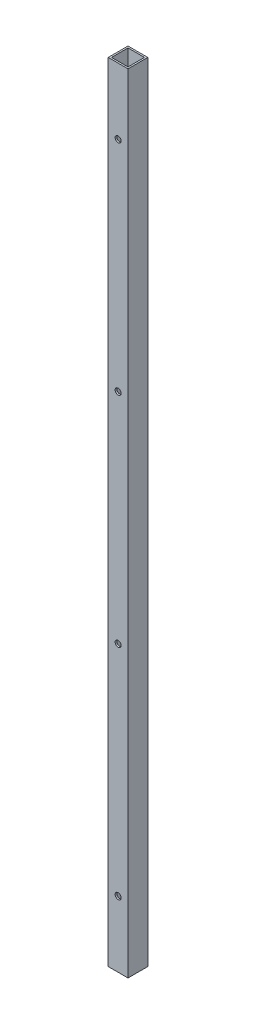
SolidWorks part; units mm, degrees
material "1060 Alloy"
ref_plane "Front Plane" through (0, 0, 0) normal (0, 0, 1) x (1, 0, 0)
ref_plane "Top Plane" through (0, 0, 0) normal (0, 1, 0) x (1, 0, 0)
ref_plane "Right Plane" through (0, 0, 0) normal (1, 0, 0) x (0, 0, -1)
sketch "Sketch1" plane through (0, 0, 0) normal (0, 1, 0) x (1, 0, 0)
  line L1 (-9.525, 9.525) -> (9.525, 9.525)
  line L2 (-9.525, 9.525) -> (-9.525, -9.525)
  line L3 (-9.525, -9.525) -> (9.525, -9.525)
  line L4 (9.525, 9.525) -> (9.525, -9.525)
  line L5 (-9.525, 9.525) -> (9.525, -9.525) construction
  line L6 (-9.525, -9.525) -> (9.525, 9.525) construction
  line L7 (-7.9375, 7.9375) -> (7.9375, 7.9375)
  line L8 (-7.9375, 7.9375) -> (-7.9375, -7.9375)
  line L9 (-7.9375, -7.9375) -> (7.9375, -7.9375)
  line L10 (7.9375, 7.9375) -> (7.9375, -7.9375)
  line L11 (-7.9375, 7.9375) -> (7.9375, -7.9375) construction
  line L12 (-7.9375, -7.9375) -> (7.9375, 7.9375) construction
  point P0 (0, 0)
  point P5 (0, 0)
  dimension "D2" = 19.05
  dimension "D1" = 19.05
  dimension "D3" = 15.875
  dimension "D4" = 15.875
extrude "Tube" add sketch "Sketch1" along normal blind 758.9266
sketch "Sketch2" plane through (0, 0, 9.525) normal (0, 0, 1) x (1, 0, 0)
  line L0 (0, 758.9266) -> (0, 777.9766) construction
  line L1 (0, 777.9766) -> (0, 781.05) construction
  line L6 (0, 695.325) -> (0, 758.9266) construction
  line L7 (-9.525, 758.9266) -> (9.525, 758.9266) construction
  circle A2 centre (0, 695.325) radius 2.8956
  dimension "D1" = 5.7912
  dimension "D2" = 19.05
  dimension "D3" = 3.0734
  dimension "D4" = 85.725
extrude "Side Wall Holes" cut sketch "Sketch2" against normal through all
pattern_linear "LPattern1" count 4 spacing 210.5745 along (0, -1, 0) of "Side Wall Holes"
sketch "Sketch3" plane through (-9.525, 0, 0) normal (-1, 0, 0) x (0, 0, 1)
  line L0 (-9.525, 758.9266) -> (9.525, 758.9266) construction
  line L1 (-123.9293, 379.4633) -> (189.6619, 379.4633) construction
  line L2 (-9.525, 0) -> (9.525, 0) construction
  circle A0 centre (0, 674.37) radius 4.7625
  circle A1 centre (0, 84.5566) radius 4.7625
  point P4 (0, 758.9266)
  dimension "D1" = 9.525
  dimension "D2" = 84.5566
extrude "Cut-Extrude1" cut sketch "Sketch3" against normal up to next and the other way through all
equation "\"Height\"= 32in"
equation "\"Width\"= 23in"
equation "\"Depth\"= 20in"
equation "\"Plexi\"= .121in"
equation "\"Cutwidth\"= .016in"
equation "\"Earsize\"= 1in + \"Cutwidth\" /2"
equation "\"Slotsize\" = 1in - \"CutWidth\" / 2"
equation "\"InnerWidth\" = \"Width\" - 2* \"Plexi\""
equation "\"InnerHeight\" = \"Height\" -2 * \"Plexi\""
equation "\"RearHoleSpacing\" = (\"Width\" - 2*\"RearHolesBorder\") / (\"RearNumHoles\"-1)"
equation "\"RivetDia\" = .228in"
equation "\"SlotDepth\" = \"Plexi\" + 0.75in + .005in"
equation "\"SideSlotWidth\"   = \"Plexi\"+.005in"
equation "\"D1@Sketch2\"=\"RivetDia\""
equation "\"D2@Sketch2\"=\"CornerCube\""
equation "\"SidePanelVertSpacing\" = (\"Height\"-2*(1.75-\"Plexi\")) / 5"
equation "\"MagnetThickness\"= 0.125in"
equation "\"MagnetDiameter\"= 12mm"
equation "\"DoorPlexi\" = \"Plexi\""
equation "\"Boxsize\" = .75in"
equation "\"Boxinner\" = .625in"
equation "\"CornerCube\" = 0.75in"
equation "\"FingerLength\" = 1.125in"
equation "\"InnerDepth\" = \"Depth\" - 2*\"Plexi\""
equation "\"RearNumHoles\" = 4"
equation "\"RearHolesBorder\" = 2.25"
equation "\"RearBarLength\" = (\"InnerWidth\"-2*\"CornerCube\")"
equation "\"RearTopNumHoles\" = 4"
equation "\"RearTopHolesBorder\" = 3.1"
equation "\"RearTopHolesSpacing\" = (\"Width\" - 2*\"RearTopHolesBorder\") / (\"RearTopNumHoles\"-1)"
equation "\"SideTopNumHoles\" = 4"
equation "\"SideTopHoleOffset\"=\"CornerCube\"+\"FingerLength\"+\"Plexi\"+.5"
equation "\"SideTopHoleSpacing\" = (\"TopBarDepth\"-2*\"SideTopHoleOffset\") / (\"SideTopNumHoles\"-1)"
equation "\"SideHorizNumHoles\" = 4"
equation "\"SideHorizHoleBorder\" = 1.50"
equation "\"SideHorizHoleSpacing\" = (\"TopBarDepth\"-2*\"SideHorizHoleBorder\") / (\"SideHorizNumHoles\"-1)"
equation "\"SideVertNumHoles\" = 4"
equation "\"SideVertHolesBorder\" = \"CornerCube\"+\"FingerLength\"+1.50"
equation "\"SideVertHoleSpacing\" = (\"SideVertBarLength\" - 2*(\"SideVertHolesBorder\"-\"Plexi\"-\"CornerCube\")) / (\"SideVertNumHoles\"-1)"
equation "\"BottomPanelSideHoleSpacing\" = (\"InnerDepth\"-2*(1.75-\"Plexi\")) / 4"
equation "\"FrontDoorGap\" = .1in"
equation "\"TopDepth\" = \"Depth\"-\"DoorPlexi\"-\"FrontDoorGap\""
equation "\"TopBarDepth\" = \"Depth\"-\"DoorPlexi\"-\"Plexi\"-2*\"MagnetThickness\"-2*\"CornerCube\""
equation "\"D3@Sketch2\"=\"Plexi\""
equation "\"D4@Sketch2\"=\"SideVertHolesBorder\""
equation "\"D3@LPattern1\"=\"SideVertHoleSpacing\""
equation "\"D1@LPattern1\"=\"SideVertNumHoles\""
equation "\"BasePlateThickness\" = 0.5in"
equation "\"SideVertBarLength\"=\"Height\"-\"BasePlateThickness\"-2*\"CornerCube\"-\"Plexi\""
equation "\"RearSideVertNumHoles\" = 4"
equation "\"RearSideVertHolesBorder\" = 2.4"
equation "\"RearSideVertHoleSpacing\" = (\"SideVertBarLength\" - 2*(\"RearSideVertHolesBorder\"-\"Plexi\"-\"CornerCube\")) / (\"RearSideVertNumHoles\"-1)"
equation "\"D1@Tube\"=\"SideVertBarLength\""
equation "\"D3@Sketch1\"=\"Boxinner\""
equation "\"D4@Sketch1\"=\"Boxinner\""
equation "\"EBWidth\" = 9in"
equation "\"BasePlateWidth\" = \"Width\"+\"EBWidth\"-2*\"Plexi\""
equation "\"BasePlateDepth\" = \"TopBarDepth\"+2*\"CornerCube\""
equation "\"BoxsizeHalf\" = \"Boxsize\"/2"
equation "\"FingerWidth\" = .625in"
equation "\"CoolerDepth\" = 12in"
equation "\"ShelfGap\" = 0.5in"
equation "\"ShelfDepth\" = \"TopBarDepth\"+\"CornerCube\"-\"CoolerDepth\""
equation "\"ShelfBarDepth\"=\"ShelfDepth\"-2*\"CornerCube\""
equation "\"ShelfWidth\" = \"EBWidth\"-\"ShelfGap\""
equation "\"ShelfBarWidth\" = \"EBWidth\"-\"Boxsize\""
equation "\"ShelfBarWidthShort\" = \"ShelfBarWidth\"-\"Boxsize\"-\"ShelfGap\""
equation "\"IntakeWidth\"=4in"
equation "\"IntakeHeight\"=2in"
equation "\"ExhaustWidth\"=4in"
equation "\"ExhaustHeight\"=2in"
equation "\"VentSpacing\"=7in"
equation "\"AngleBracketLength\"=20mm"
equation "\"AngleBracketWidth\"=.5in"
equation "\"AngleBracketThickness\"=.125in"
equation "\"AngleBracketHolePos\"=15mm"
equation "\"AngleBracketHoleDia\"=\"Rivet3_16Dia\""
equation "\"ShelfBarAngleHole\"=\"ShelfGap\"+\"Boxsize\"+\"AngleBracketHolePosShort\""
